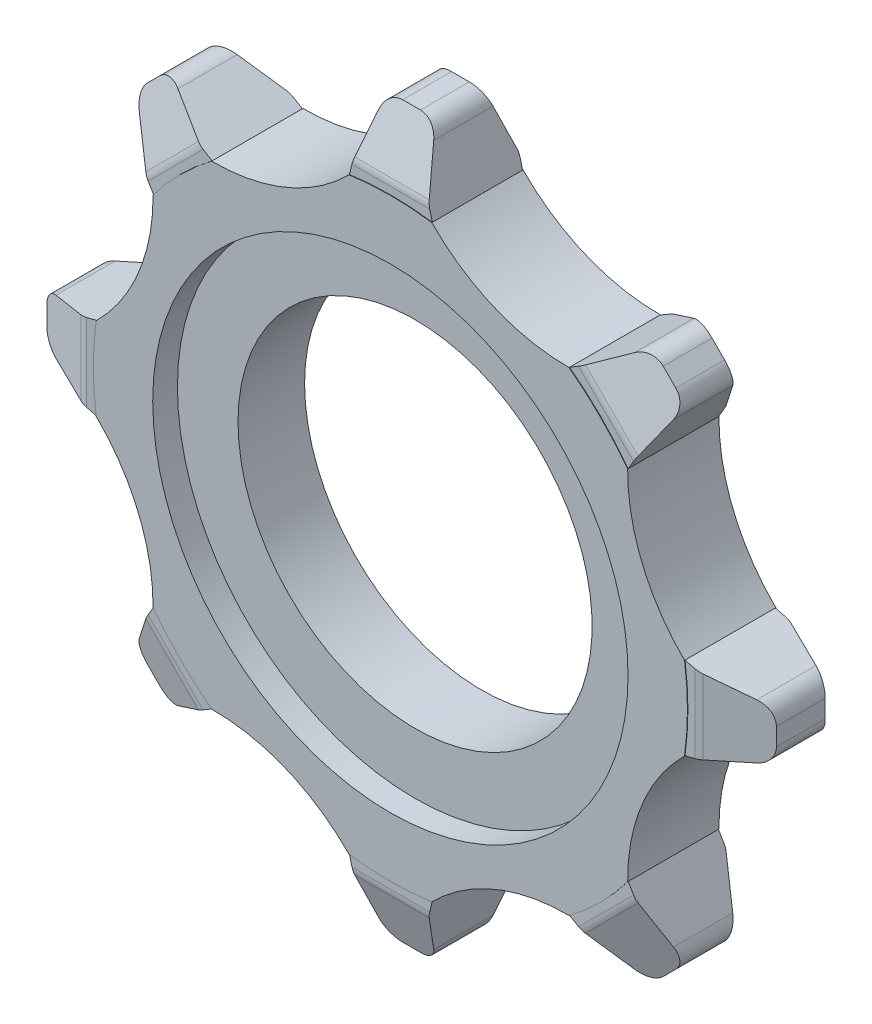
SolidWorks part; units mm, degrees
other "Markup1"
sketch "Sketch4" plane through (-30, 25, -15) normal (-0.7934, 0.0966, -0.601) x (-0.1502, -0.9879, 0.0395)
ref_plane "Front Plane" through (0, 0, 0) normal (0, 0, 1) x (1, 0, 0)
ref_plane "Top Plane" through (0, 0, 0) normal (0, 1, 0) x (1, 0, 0)
ref_plane "Right Plane" through (0, 0, 0) normal (1, 0, 0) x (0, 0, -1)
sketch "Sketch1" plane through (0, 0, 0) normal (0, 0, 1) x (1, 0, 0)
  line L0 (0, 0) -> (-50000, 0) construction
  circle A0 centre (0, 0) radius 31.25
  dimension "D1" = 62.5
extrude "Boss-Extrude1" add sketch "Sketch1" along normal mid plane 30
sketch "Sketch2" plane through (0, 0, 0) normal (0, 0, 1) x (1, 0, 0)
  line L0 (10.9478, 0) -> (-49989.0522, 0) construction
  line L1 (-28.3721, -5) -> (-28.3721, 5)
  line L2 (-28.3721, -5) -> (-38.3721, -2.5)
  line L3 (-28.3721, 5) -> (-38.3721, 2.5)
  line L4 (-38.3721, 2.5) -> (-38.3721, -2.5)
  line L5 (-33.6569, -15.7864) -> (-33.0873, 15.7864) construction
  point P6 (-28.3721, 0)
  point P13 (-33.3721, 0)
  dimension "D3" = 5
  dimension "D1" = 10
  dimension "D2" = 10
  dimension "D4" = 5
extrude "Boss-Extrude2" add sketch "Sketch2" along normal mid plane 9.5
sketch "Sketch8" plane through (0, 0, -15) normal (0, 0, -1) x (-1, 0, 0)
  line L0 (38.3721, 2.5) -> (38.3721, -2.5) construction
  line L1 (38.3721, 4.3667) -> (36.1221, 4.3667)
  line L2 (38.3721, 4.3667) -> (38.3721, -4.3553)
  line L3 (38.3721, -4.3553) -> (36.1221, -4.3553)
  line L4 (36.1221, 4.3667) -> (36.1221, -4.3553)
  dimension "D1" = 2.25
extrude "Cut-Extrude5" [suppressed] cut sketch "Sketch8" against normal blind 31
ref_plane "Plane2" through (0, 0, 0) normal (0, 1, 0) x (1, 0, 0)
chamfer "Chamfer1" distance 6 angle 20 1 edges at (-38.3721, 0, -4.75)
chamfer "Chamfer2" distance 6 angle 20 1 edges at (-38.3721, 0, 4.75)
fillet "Fillet11" radius 2 2 edges at (-38.3721, -2.5, 0) (-38.3721, 2.5, 0)
fillet "Fillet12" radius 2 2 edges at (-32.3721, 0, 4.75) (-32.3721, 0, -4.75)
pattern_circular "CirPattern1" count 8 over 360 about axis through (0, 0, 0) along (0, 0, 1) of "Boss-Extrude2", "Fillet11", "Chamfer1", "Chamfer2", "Fillet12"
sketch "Sketch3" [suppressed] plane through (0, 0, 15) normal (0, 0, 1) x (1, 0, 0)
  line L0 (5.5, 5.5) -> (-5.5, 5.5) construction
  line L5 (-5.5, 5.5) -> (5.5, -5.5) construction
  line L6 (-5.5, -5.5) -> (5.5, 5.5) construction
  line L7 (-5.5, 5.5) -> (-5.5, -5.5) construction
  line L8 (5.5, 5.5) -> (5.5, -5.5) construction
  line L9 (5.5, -5.5) -> (-5.5, -5.5) construction
  circle A0 centre (0, 0) radius 2.5
  circle A1 centre (5.5, 5.5) radius 2
  circle A2 centre (-5.5, 5.5) radius 2
  circle A3 centre (-5.5, -5.5) radius 2
  circle A4 centre (5.5, -5.5) radius 2
  dimension "D1" = 5
  dimension "D4" = 4
  dimension "D5" = 4
  dimension "D6" = 4
  dimension "D7" = 4
  dimension "D2" = 11
  dimension "D3" = 11
extrude "Cut-Extrude6" [suppressed] cut sketch "Sketch3" against normal through all
ref_point "Point1" [suppressed]
sketch "Sketch12" [suppressed] plane through (0, 0, -15) normal (0, 0, -1) x (-1, 0, 0)
  circle A0 centre (0, 0) radius 18.625
  dimension "D1" = 37.25
extrude "Cut-Extrude10" [suppressed] cut sketch "Sketch12" against normal blind 18
sketch "Sketch9" [suppressed] plane through (0, 0, -15) normal (0, 0, -1) x (-1, 0, 0)
  circle A0 centre (0, 0) radius 14.5
  dimension "D1" = 29
extrude "Cut-Extrude7" [suppressed] cut sketch "Sketch9" against normal offset from surface (10 mm away) 20
sketch "Sketch11" [suppressed] plane through (0, 0, -15) normal (0, 0, -1) x (-1, 0, 0)
  circle A0 centre (0, 0) radius 25
  circle A1 centre (0, 0) radius 14.5 construction
  circle A2 centre (0, 0) radius 14.5
  dimension "D1" = 50
extrude "Cut-Extrude9" [suppressed] cut sketch "Sketch11" against normal offset from surface (23 mm away) 7
fillet "Fillet9" [suppressed] radius 10
fillet "Fillet10" [suppressed] radius 2
sketch "Sketch13" [suppressed] plane through (0, 0, 3) normal (0, 0, -1) x (-1, 0, 0)
  circle A3 centre (0, 0) radius 15.125
  circle A4 centre (0, 0) radius 15.125
  circle A5 centre (0, 0) radius 18.625 construction
  circle A6 centre (0, 0) radius 18.625
  dimension "D1" = 3.5
extrude "Boss-Extrude3" [suppressed] add sketch "Sketch13" along normal offset from surface (11 mm away) 7
ref_plane "Plane3" through (0, 0, -4.8) normal (0, 0, -1) x (-1, 0, 0)
ref_plane "Plane4" through (0, 0, 4.8) normal (0, 0, 1) x (1, 0, 0)
sketch "Sketch14" plane through (0, 0, -4.8) normal (0, 0, -1) x (-1, 0, 0)
  line L1 (-46.4868, 40.1571) -> (68.2948, 40.1571)
  line L2 (-46.4868, 40.1571) -> (-46.4868, -59.8251)
  line L3 (-46.4868, -59.8251) -> (68.2948, -59.8251)
  line L4 (68.2948, 40.1571) -> (68.2948, -59.8251)
extrude "Cut-Extrude11" cut sketch "Sketch14" along normal blind 20
sketch "Sketch15" plane through (0, 0, 4.8) normal (0, 0, 1) x (1, 0, 0)
  line L1 (-95.8823, 60.4837) -> (98.5269, 60.4837)
  line L2 (-95.8823, 60.4837) -> (-95.8823, -68.9951)
  line L3 (-95.8823, -68.9951) -> (98.5269, -68.9951)
  line L4 (98.5269, 60.4837) -> (98.5269, -68.9951)
extrude "Cut-Extrude12" cut sketch "Sketch15" along normal blind 20
sketch "Sketch17" plane through (0, 0, 4.8) normal (0, 0, 1) x (1, 0, 0)
  line L0 (-3.9172, 32.7035) -> (-4.3568, 30.9448)
  line L1 (-20.355, 25.8947) -> (-18.8005, 24.962)
  line L2 (-20.355, 25.8947) -> (-3.9172, 32.7035)
  arc A0 (-18.8005, 24.962) -> (-4.3568, 30.9448) centre (-18.6236, 44.9612) ccw
extrude "Cut-Extrude13" cut sketch "Sketch17" against normal blind 20
pattern_circular "CirPattern3" count 8 over 360 about axis through (0, 0, 0) along (0, 0, 1) of "Cut-Extrude13"
sketch "Sketch20" plane through (0, 0, 4.8) normal (0, 0, 1) x (1, 0, 0)
  circle A0 centre (0, 0) radius 18.625
  dimension "D1" = 37.25
extrude "Cut-Extrude14" cut sketch "Sketch20" against normal blind 20
sketch "Sketch21" plane through (0, 0, 4.8) normal (0, 0, 1) x (1, 0, 0)
  circle A0 centre (0, 0) radius 25
  dimension "D1" = 50
extrude "Cut-Extrude15" cut sketch "Sketch21" against normal offset from surface (2.6 mm away) 7 up to face at (-18.625, 0, -4.8)
